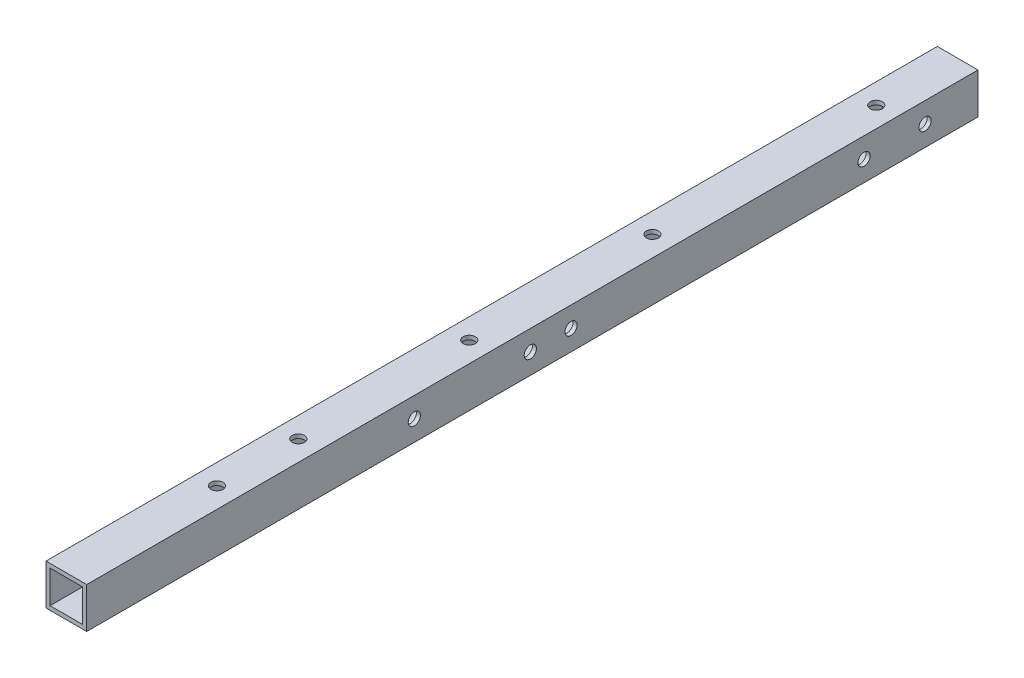
SolidWorks part; units mm, degrees
material "6063-O"
ref_plane "前视基准面" through (0, 0, 0) normal (0, 0, 1) x (1, 0, 0)
ref_plane "上视基准面" through (0, 0, 0) normal (0, 1, 0) x (1, 0, 0)
ref_plane "右视基准面" through (0, 0, 0) normal (1, 0, 0) x (0, 0, -1)
other "Configuration Table"
sketch "草图1" plane through (0, 0, 0) normal (0, 0, 1) x (1, 0, 0)
  line L1 (-5, -5) -> (5, -5)
  line L2 (-5, -5) -> (-5, 5)
  line L3 (-5, 5) -> (5, 5)
  line L4 (5, -5) -> (5, 5)
  line L5 (-5, -5) -> (5, 5) construction
  line L6 (-5, 5) -> (5, -5) construction
  point P4 (0, 0)
  dimension "D1" = 10
  dimension "D2" = 10
extrude "拉伸-薄壁1" add sketch "草图1" along normal blind 219 thin thin type one direction reverse wall 1
sketch "草图2" plane through (0, 5, 0) normal (0, 1, 0) x (1, 0, 0)
  line L0 (0, -219) -> (0, 0) construction
  line L1 (5, -219) -> (-5, -219) construction
  line L2 (5, 0) -> (-5, 0) construction
  line L3 (-5, -120) -> (5, -120) construction
  line L4 (-5, -219) -> (-5, 0) construction
  line L5 (5, -219) -> (5, 0) construction
  circle A0 centre (0, -140) radius 1.5 construction
  circle A1 centre (0, -182) radius 1.5
  circle A3 centre (0, -20) radius 1.5
  circle A4 centre (0, -120) radius 1.5
  circle A5 centre (0, -120) radius 1.5 construction
  circle A6 centre (0, -162) radius 1.5
  circle A8 centre (0, -75) radius 1.5
  point P10 (5, -120)
  dimension "D1" = 3
  dimension "D2" = 20
  dimension "D3" = 42
  dimension "D4" = 3
  dimension "D6" = 0
  dimension "D7" = 20
  dimension "D8" = 20
  dimension "D9" = 75
  dimension "D5" = 120
extrude "切除-拉伸1" cut sketch "草图2" against normal blind 10
sketch "草图3" plane through (5, 0, 0) normal (1, 0, 0) x (0, 0, -1)
  line L0 (0, 0) -> (-219, 0) construction
  line L1 (0, -5) -> (0, 5) construction
  line L2 (-219, -5) -> (-219, 5) construction
  circle A0 centre (-13, 0) radius 1.5
  circle A1 centre (-28, 0) radius 1.5
  circle A2 centre (-138.5, 0) radius 1.5
  circle A3 centre (-100, 0) radius 1.5
  circle A4 centre (-110, 0) radius 1.5
  dimension "D1" = 3
  dimension "D3" = 15
  dimension "D4" = 138.5
  dimension "D5" = 28.5
  dimension "D6" = 10
  dimension "D2" = 13
extrude "切除-拉伸2" cut sketch "草图3" against normal through all
